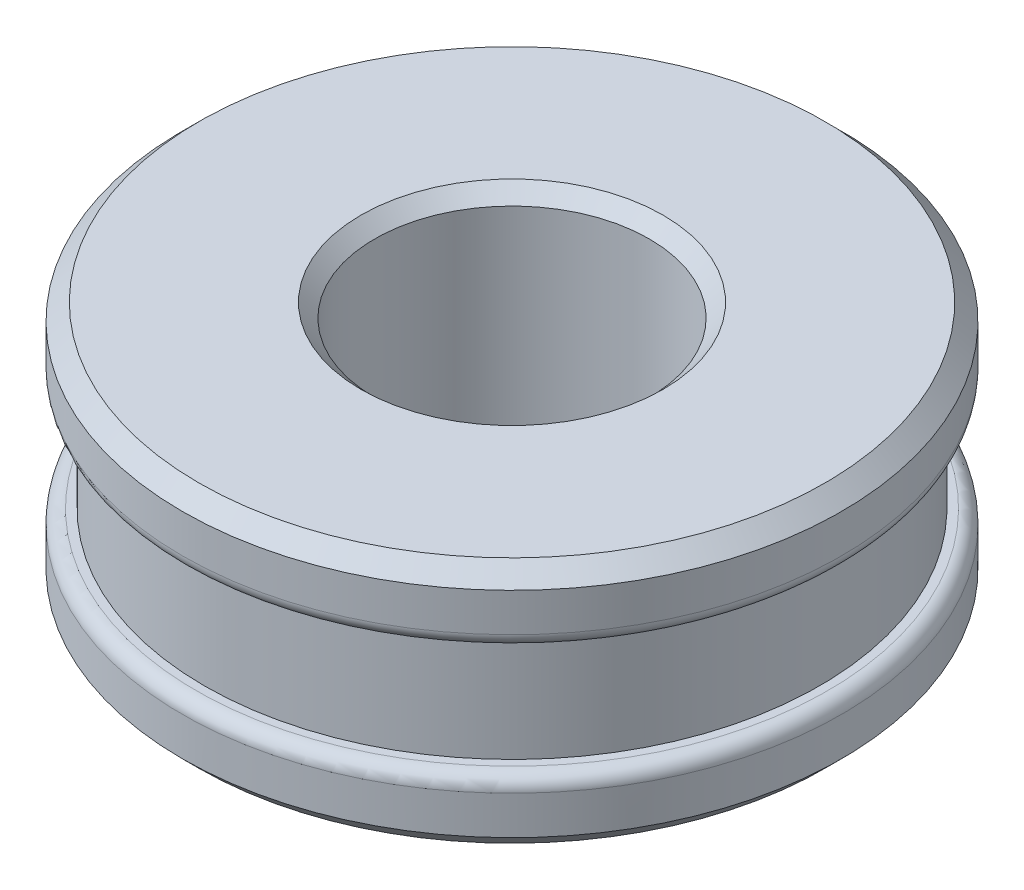
SolidWorks part; units mm, degrees
ref_plane "前视基准面" through (0, 0, 0) normal (0, 0, 1) x (1, 0, 0)
ref_plane "上视基准面" through (0, 0, 0) normal (0, 1, 0) x (1, 0, 0)
ref_plane "右视基准面" through (0, 0, 0) normal (1, 0, 0) x (0, 0, -1)
sketch "草图1" plane through (0, 0, 0) normal (0, 1, 0) x (1, 0, 0)
  circle A0 centre (0, 0) radius 5
  circle A1 centre (0, 0) radius 12
  dimension "D1" = 10
  dimension "D2" = 24
extrude "凸台-拉伸1" add sketch "草图1" along normal blind 9
chamfer "倒角1" distance 0.6 angle 45 2 edges at (0, 0, 12) (0, 9, 12)
sketch "草图2" plane through (0, 0, 0) normal (0, 0, 1) x (1, 0, 0)
  line L0 (12, 6.5) -> (11.2, 6.5)
  line L1 (12, 0.6) -> (12, 8.4) construction
  line L2 (11.2, 6.5) -> (11.2, 2.5)
  line L3 (11.2, 2.5) -> (12, 2.5)
  line L4 (12, 2.5) -> (14.676, 3.7349)
  line L5 (14.676, 3.7349) -> (12, 6.5)
  line L6 (11.4, 9) -> (-11.4, 9) construction
  line L7 (-11.4, 0) -> (11.4, 0) construction
  line L8 (0, 0) -> (0, 26.2819) construction
  dimension "D1" = 2.5
  dimension "D2" = 2.5
  dimension "D3" = 0.8
revolve "切除-旋转1" cut sketch "草图2" angle 360 about L8
fillet "圆角1" radius 0.5 2 edges at (0, 6.5, -12) (0, 2.5, -12)
chamfer "倒角2" distance 0.5 angle 45 2 edges at (0, 0, 5) (0, 9, 5)
